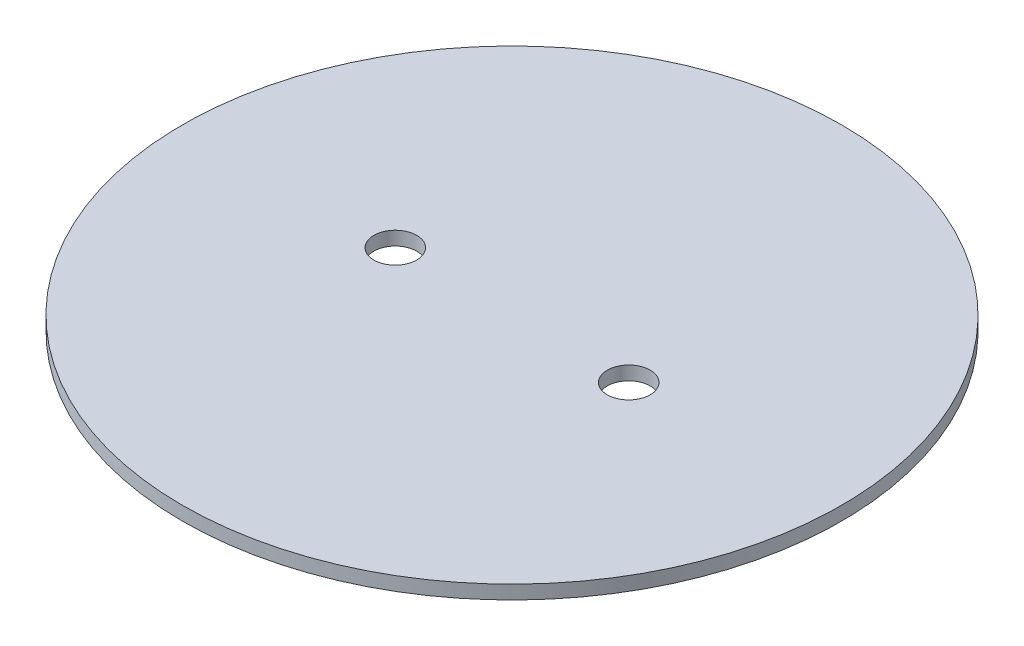
SolidWorks part; units mm, degrees
ref_plane "Front Plane" through (0, 0, 0) normal (0, 0, 1) x (1, 0, 0)
ref_plane "Top Plane" through (0, 0, 0) normal (0, 1, 0) x (1, 0, 0)
ref_plane "Right Plane" through (0, 0, 0) normal (1, 0, 0) x (0, 0, -1)
sketch "Sketch1" plane through (0, 0, 0) normal (0, 1, 0) x (1, 0, 0)
  line L0 (-26.9875, 0) -> (26.9875, 0) construction
  circle A0 centre (0, 0) radius 76.2
  circle A1 centre (26.9875, 0) radius 4.953
  circle A2 centre (-26.9875, 0) radius 4.953
  dimension "D1" = 152.4
  dimension "D4" = 9.906
  dimension "D2" = 53.975
extrude "Boss-Extrude1" add sketch "Sketch1" along normal blind 3.175
